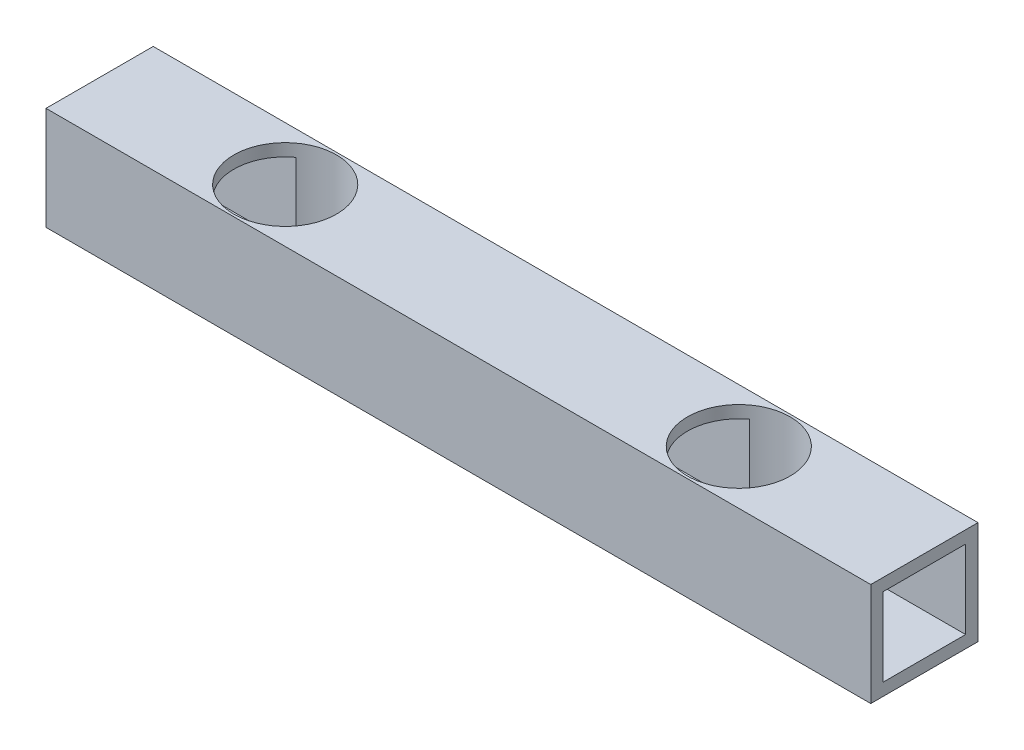
SolidWorks part; units mm, degrees
ref_plane "Front Plane" through (0, 0, 0) normal (0, 0, 1) x (1, 0, 0)
ref_plane "Top Plane" through (0, 0, 0) normal (0, 1, 0) x (1, 0, 0)
ref_plane "Right Plane" through (0, 0, 0) normal (1, 0, 0) x (0, 0, -1)
sketch "Sketch1" plane through (0, 0, 0) normal (0, 1, 0) x (1, 0, 0)
  line L0 (-100, 13) -> (100, -13) construction
  line L1 (-100, 13) -> (100, 13)
  line L2 (-100, 13) -> (-100, -13)
  line L3 (-100, -13) -> (100, -13)
  line L4 (100, 13) -> (100, -13)
  dimension "D1" = 200
  dimension "D2" = 26
extrude "Boss-Extrude1" add sketch "Sketch1" along normal blind 25
shell "Shell1" thickness 3
sketch "Sketch2" plane through (0, 25, 0) normal (0, 1, 0) x (1, 0, 0)
  line L0 (0, 0) -> (0, -13) construction
  line L1 (-100, -13) -> (100, -13) construction
  circle A0 centre (-55, 0) radius 12.45
  circle A1 centre (55, 0) radius 12.45
  dimension "D1" = 13
  dimension "D2" = 55
extrude "Cut-Extrude1" cut sketch "Sketch2" against normal blind 25
